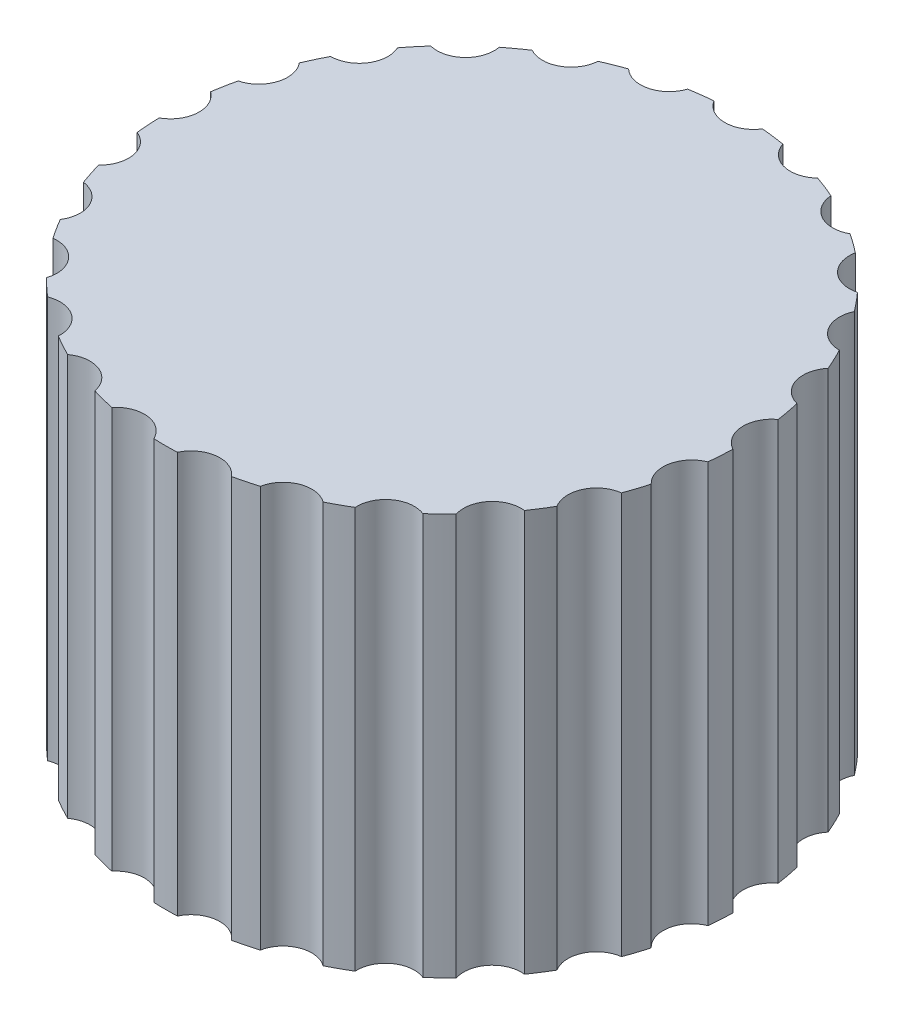
SolidWorks part; units mm, degrees
ref_plane "Plan de face" through (0, 0, 0) normal (0, 0, 1) x (1, 0, 0)
ref_plane "Plan de dessus" through (0, 0, 0) normal (0, 1, 0) x (1, 0, 0)
ref_plane "Plan de droite" through (0, 0, 0) normal (1, 0, 0) x (0, 0, -1)
sketch "Esquisse1" plane through (0, 0, 0) normal (0, 1, 0) x (1, 0, 0)
  line L0 (-2.641, -1.475) -> (2.641, -1.475)
  line L1 (0, 3.025) -> (0, -1.475) construction
  circle A0 centre (0, 0) radius 10
  circle A1 centre (0, 0) radius 3.025
  dimension "D1" = 20
  dimension "D2" = 4.5
  dimension "D3" = 6.05
extrude "Boss.-Extru.1" add sketch "Esquisse1" along normal blind 12 contours A0 A1 | L0 A1
sketch "Esquisse2" plane through (0, 12, 0) normal (0, 1, 0) x (1, 0, 0)
  circle A0 centre (0, 0) radius 10
extrude "Boss.-Extru.2" add sketch "Esquisse2" along normal blind 2
sketch "Esquisse3" plane through (0, 14, 0) normal (0, 1, 0) x (1, 0, 0)
  circle A0 centre (0, 10.5) radius 1
  dimension "D1" = 2
  dimension "D2" = 10.5
extrude "Enlèv. mat.-Extru.1" cut sketch "Esquisse3" against normal through all
pattern_circular "Répétition circulaire1" count 25 over 360 about axis through (0, 0, 0) along (0, 1, 0) of "Enlèv. mat.-Extru.1"
